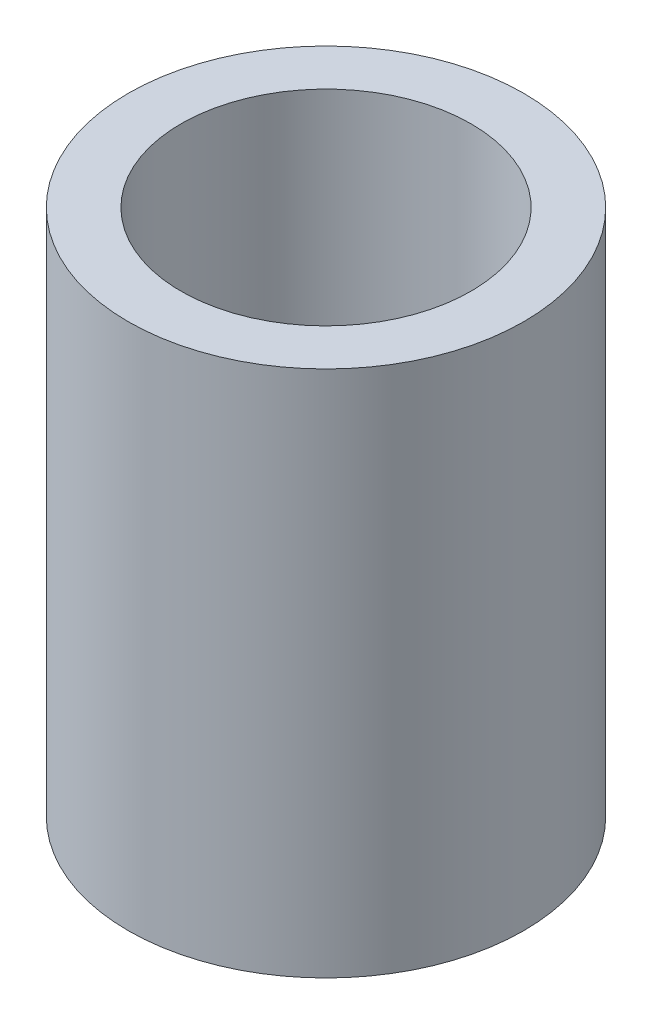
SolidWorks part; units mm, degrees
material "Copper"
ref_plane "Front Plane" through (0, 0, 0) normal (0, 0, 1) x (1, 0, 0)
ref_plane "Top Plane" through (0, 0, 0) normal (0, 1, 0) x (1, 0, 0)
ref_plane "Right Plane" through (0, 0, 0) normal (1, 0, 0) x (0, 0, -1)
sketch "Sketch1" plane through (0, 0, 0) normal (0, 0, 1) x (1, 0, 0)
  line L0 (0, 0) -> (1.1, 0) construction
  line L1 (1.1, 0) -> (1.5, 0)
  line L2 (1.1, 0) -> (1.1, 4)
  line L3 (1.1, 4) -> (1.5, 4)
  line L4 (1.5, 0) -> (1.5, 4)
  line L5 (0, 0) -> (0, 7.7064) construction
  dimension "D1" = 4
  dimension "D2" = 3
  dimension "D3" = 2.2
revolve "Revolve1" add sketch "Sketch1" angle 360 about L5
